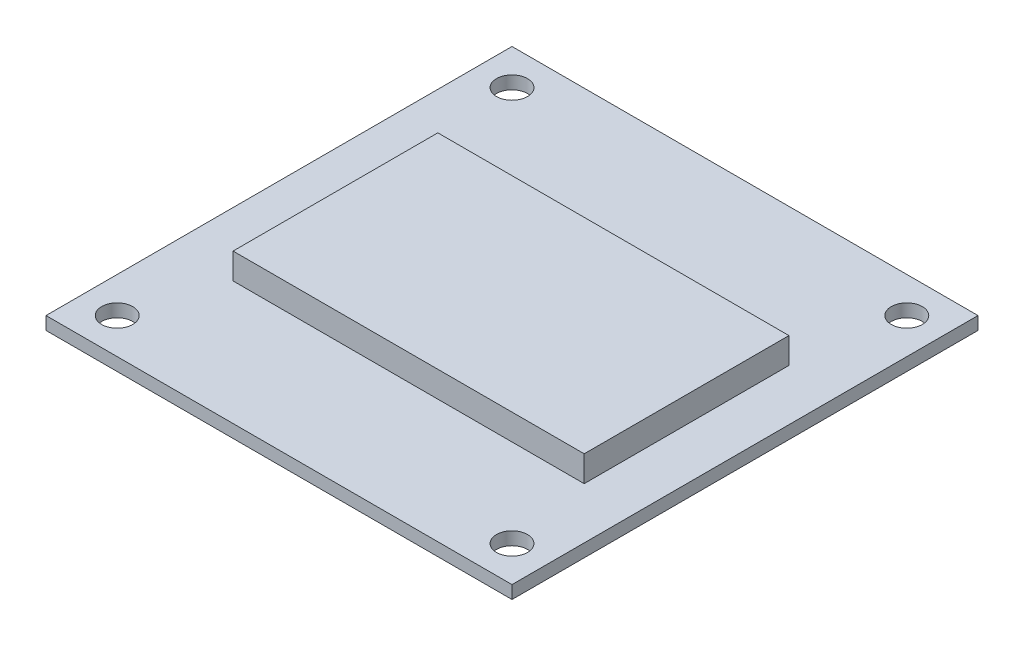
SolidWorks part; units mm, degrees
ref_plane "Plan de face" through (0, 0, 0) normal (0, 0, 1) x (1, 0, 0)
ref_plane "Plan de dessus" through (0, 0, 0) normal (0, 1, 0) x (1, 0, 0)
ref_plane "Plan de droite" through (0, 0, 0) normal (1, 0, 0) x (0, 0, -1)
sketch "Esquisse1" plane through (0, 0, 0) normal (0, 1, 0) x (1, 0, 0)
  line L1 (0, 0) -> (36, 0)
  line L2 (0, 0) -> (0, 36)
  line L3 (0, 36) -> (36, 36)
  line L4 (36, 0) -> (36, 36)
  dimension "D1" = 36
  dimension "D2" = 36
extrude "Boss.-Extru.1" add sketch "Esquisse1" along normal blind 1
hole_wizard "Dégagement M21" positions "Esquisse2" profile "Esquisse3" size "M2" standard "ISO" slot yes end condition through all
sketch "Esquisse2" plane through (0, 1, 0) normal (0, 1, 0) x (1, 0, 0)
  line L0 (0, 36) -> (0, 0) construction
  line L1 (0, 0) -> (36, 0) construction
  line L10 (36, 0) -> (36, 36) construction
  point P0 (2.75, 2.75)
  point P2 (2.75, 33.25)
  point P4 (33.25, 33.25)
  point P6 (33.25, 2.75)
  point P13 (2.9278, 33.9996)
  point P22 (33.25, 2.75)
  dimension "D1" = 30.5
  dimension "D2" = 30.5
  dimension "D3" = 30.5
  dimension "D4" = 30.5
  dimension "D5" = 2.75
  dimension "D6" = 2.75
  dimension "D7" = 2.75
  dimension "D8" = 2.75
sketch "Esquisse3" plane through (2.75, 1, -2.75) normal (1, 0, 0) x (0, 0, 1)
  line L0 (0, 0) -> (0, 1)
  line L1 (0, 1) -> (1.2, 1)
  line L2 (1.2, 1) -> (1.2, 0)
  line L5 (1.2, 0) -> (0, 0)
  line L11 (0, -6.35) -> (0, 107.95) construction
  dimension "Diamètre du perçage jusqu'au prochain" = 2.4
  dimension "Profondeur du perçage jusqu'au prochain" = 1
sketch "Esquisse4" plane through (0, 1, 0) normal (0, 1, 0) x (1, 0, 0)
  line L1 (4.9125, 25.3572) -> (32.0379, 25.3572)
  line L2 (4.9125, 25.3572) -> (4.9125, 9.5395)
  line L3 (4.9125, 9.5395) -> (32.0379, 9.5395)
  line L4 (32.0379, 25.3572) -> (32.0379, 9.5395)
extrude "Boss.-Extru.2" add sketch "Esquisse4" along normal blind 2
